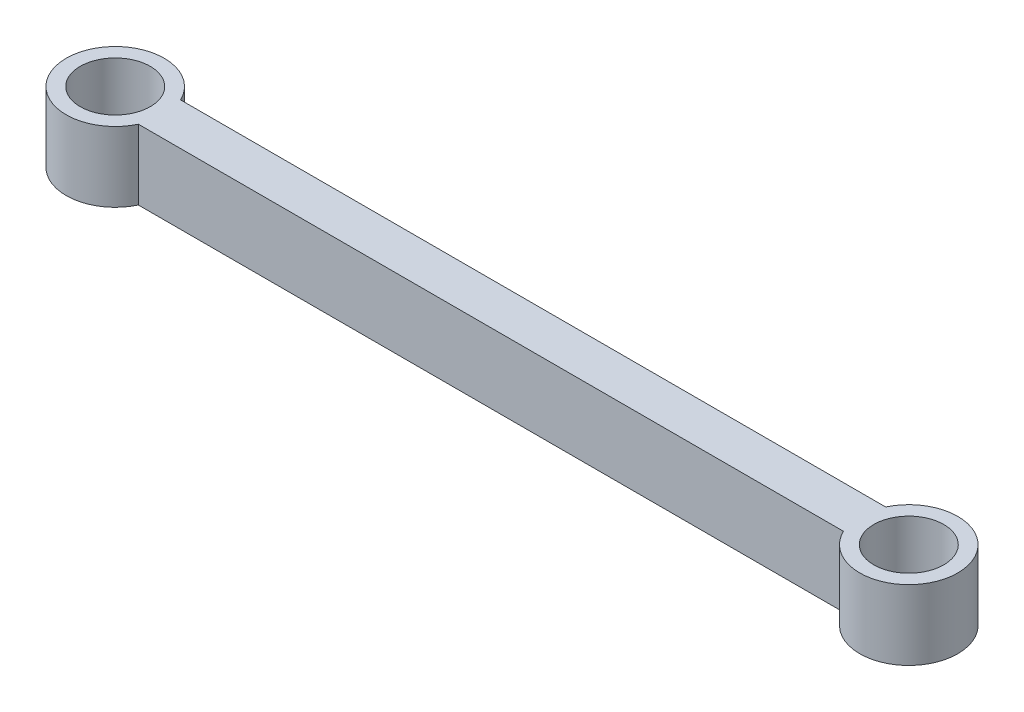
SolidWorks part; units mm, degrees
ref_plane "Plan de face" through (0, 0, 0) normal (0, 0, 1) x (1, 0, 0)
ref_plane "Plan de dessus" through (0, 0, 0) normal (0, 1, 0) x (1, 0, 0)
ref_plane "Plan de droite" through (0, 0, 0) normal (1, 0, 0) x (0, 0, -1)
sketch "Esquisse1" plane through (0, 0, 0) normal (0, 1, 0) x (1, 0, 0)
  line L0 (63.2001, 30.0955) -> (1070.3069, 30.0955)
  line L1 (63.2001, -30.0955) -> (1070.3069, -30.0955)
  circle A1 centre (0, 0) radius 70
  circle A2 centre (1133.5071, 0) radius 70
  dimension "D3" = 140
  dimension "D4" = 140
  dimension "D1" = 1007.1068
  dimension "D2" = 1007.1068
extrude "Boss.-Extru.2" add sketch "Esquisse1" along normal blind 100 contours A2 L0 A1 L1 | A1 | A2
sketch "Esquisse2" plane through (0, 100, 0) normal (0, 1, 0) x (1, 0, 0)
  circle A0 centre (0, 0) radius 50
extrude "Enlèv. mat.-Extru.2" cut sketch "Esquisse2" against normal blind 95
sketch "Esquisse4" plane through (0, 100, 0) normal (0, 1, 0) x (1, 0, 0)
  circle A0 centre (1133.5071, 0) radius 50
extrude "Enlèv. mat.-Extru.3" cut sketch "Esquisse4" against normal through all contours A0
equation "\"D1@Esquisse1\"=(sqr(2)/2)+0.3"
equation "\"D2@Esquisse1\"=\"D1@Esquisse1\""
equation "\"D3@Esquisse1\"=\"D4@Esquisse1\""
